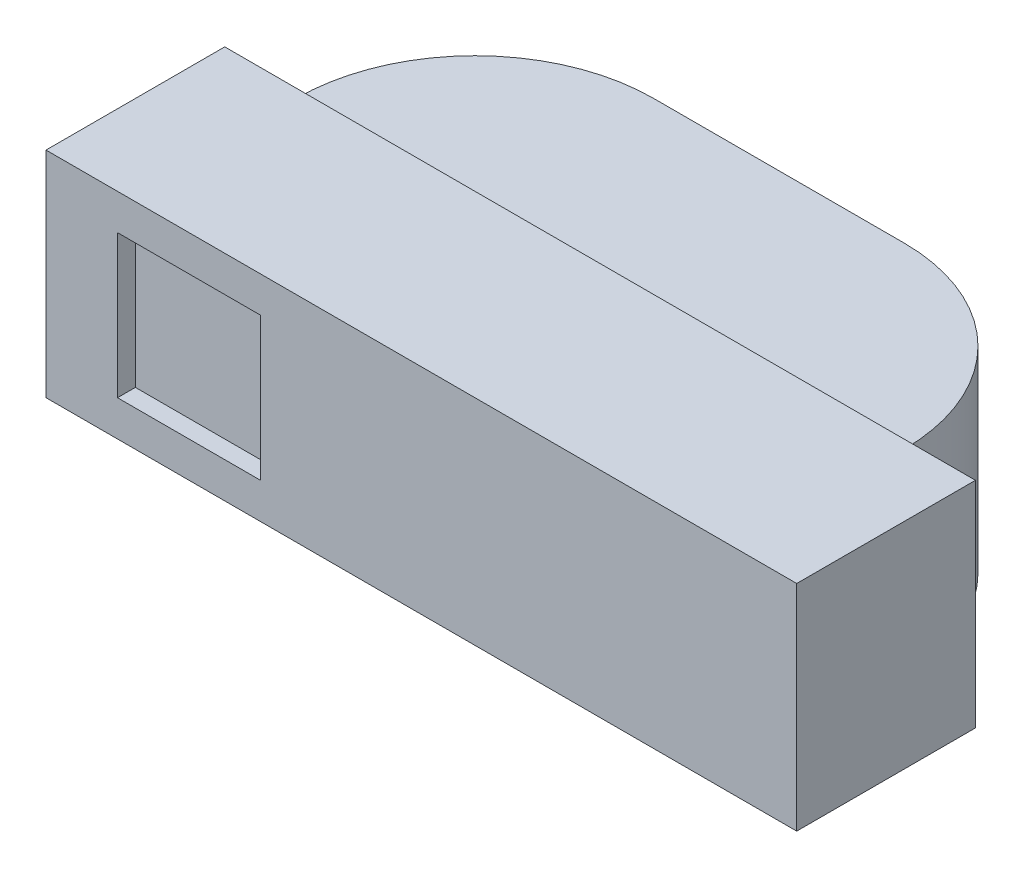
SolidWorks part; units mm, degrees
ref_plane "Front Plane" through (0, 0, 0) normal (0, 0, 1) x (1, 0, 0)
ref_plane "Top Plane" through (0, 0, 0) normal (0, 1, 0) x (1, 0, 0)
ref_plane "Right Plane" through (0, 0, 0) normal (1, 0, 0) x (0, 0, -1)
sketch "Sketch1" plane through (0, 0, 0) normal (0, 1, 0) x (1, 0, 0)
  line L1 (-1.05, -0.5) -> (1.05, -0.5)
  line L2 (-1.05, -0.5) -> (-1.05, 0)
  line L3 (-1.05, 0) -> (-0.85, 0)
  line L4 (1.05, -0.5) -> (1.05, 0)
  line L5 (-0.35, 0.5) -> (0.35, 0.5)
  line L6 (0.85, 0) -> (1.05, 0)
  arc A0 (-0.35, 0.5) -> (-0.85, 0) centre (-0.35, 0) ccw
  arc A1 (0.85, 0) -> (0.35, 0.5) centre (0.35, 0) ccw
  dimension "D4" = 1.7
  dimension "D1" = 2.1
  dimension "D2" = 0.5
  dimension "D3" = 0.5
  dimension "D5" = 0.85
  dimension "D6" = 1.05
extrude "Boss-Extrude1" add sketch "Sketch1" along normal blind 0.6
sketch "Sketch2" plane through (0, 0, -0.5) normal (0, 0, -1) x (-1, 0, 0)
  line L0 (1.05, 0.6) -> (1.05, 0) construction
  line L1 (-1.05, 0.6) -> (1.05, 0.6)
  line L2 (-1.05, 0.6) -> (-1.05, 0.575)
  line L3 (-1.05, 0.575) -> (1.05, 0.575)
  line L4 (1.05, 0.6) -> (1.05, 0.575)
  line L6 (-1.05, 0) -> (1.05, 0)
  line L7 (-1.05, 0) -> (-1.05, 0.025)
  line L8 (-1.05, 0.025) -> (1.05, 0.025)
  line L9 (1.05, 0) -> (1.05, 0.025)
  dimension "D1" = 0.025
  dimension "D2" = 0.025
extrude "Cut-Extrude1" cut sketch "Sketch2" against normal blind 0.5
sketch "Sketch3" plane through (0, 0, 0.5) normal (0, 0, 1) x (1, 0, 0)
  line L0 (-1.05, 0.6) -> (-1.05, 0) construction
  line L1 (-0.85, 0.5) -> (-0.45, 0.5)
  line L2 (-0.85, 0.5) -> (-0.85, 0.1)
  line L3 (-0.85, 0.1) -> (-0.45, 0.1)
  line L4 (-0.45, 0.5) -> (-0.45, 0.1)
  line L5 (-1.05, 0.6) -> (1.05, 0.6) construction
  line L6 (-1.05, 0) -> (1.05, 0) construction
  dimension "D1" = 0.2
  dimension "D2" = 0.1
  dimension "D3" = 0.4
  dimension "D4" = 0.1
extrude "Cut-Extrude2" cut sketch "Sketch3" against normal blind 0.05
